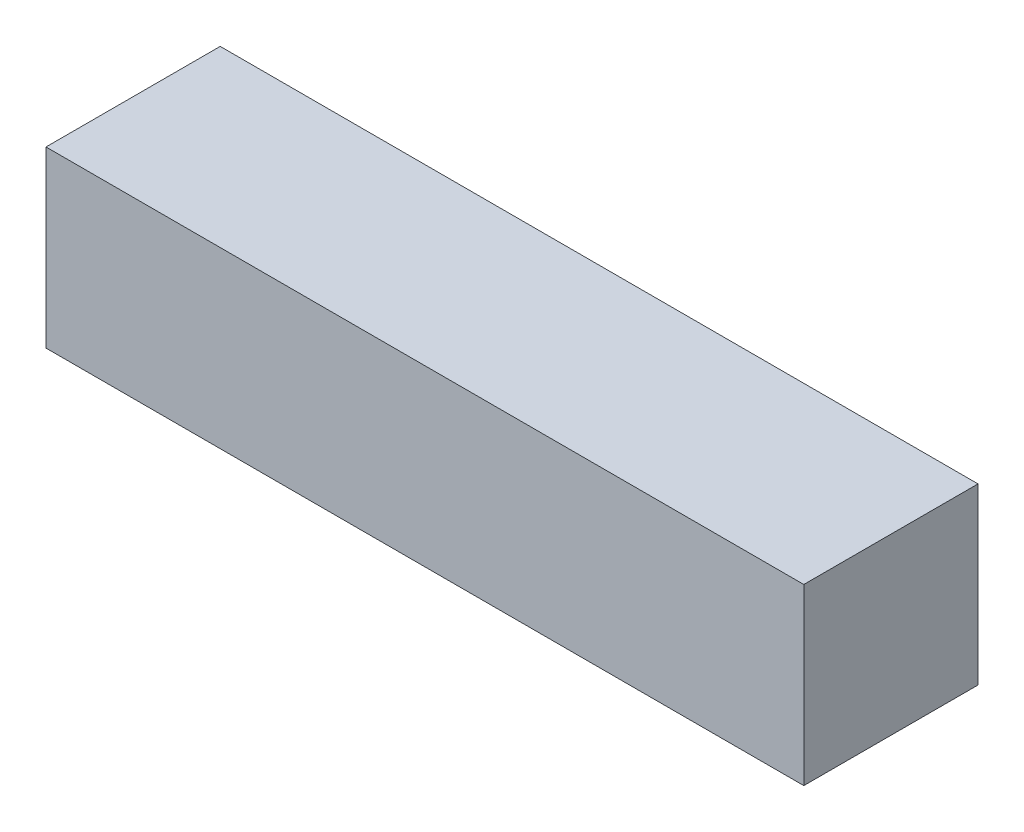
SolidWorks part; units mm, degrees
material "鎳"
ref_plane "前基準面" through (0, 0, 0) normal (0, 0, 1) x (1, 0, 0)
ref_plane "上基準面" through (0, 0, 0) normal (0, 1, 0) x (1, 0, 0)
ref_plane "右基準面" through (0, 0, 0) normal (1, 0, 0) x (0, 0, -1)
sketch "草圖1" plane through (0, 0, 0) normal (0, 0, 1) x (1, 0, 0)
  line L1 (-43.5, 10) -> (43.5, 10)
  line L2 (-43.5, 10) -> (-43.5, -10)
  line L3 (-43.5, -10) -> (43.5, -10)
  line L4 (43.5, 10) -> (43.5, -10)
  line L5 (-43.5, 10) -> (43.5, -10) construction
  line L6 (-43.5, -10) -> (43.5, 10) construction
  point P0 (0, 0)
  dimension "D1" = 87
  dimension "D2" = 20
extrude "填料-伸長1" add sketch "草圖1" along normal blind 20
sketch3d "URDF Reference"
  line L0 (0, 0, 0) -> (10, 0, 0) construction
  line L1 (0, 0, 0) -> (0, 0, -10) construction
  point P0 (0, 0, 0)
  point P1 (0, 0, 0)
